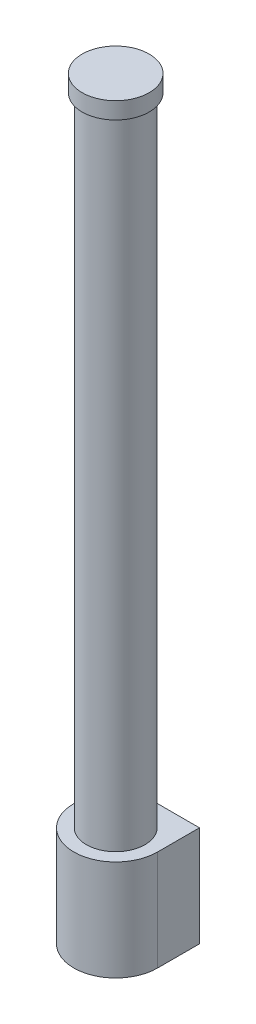
SolidWorks part; units mm, degrees
ref_plane "Front Plane" through (0, 0, 0) normal (0, 0, 1) x (1, 0, 0)
ref_plane "Top Plane" through (0, 0, 0) normal (0, 1, 0) x (1, 0, 0)
ref_plane "Right Plane" through (0, 0, 0) normal (1, 0, 0) x (0, 0, -1)
sketch "Sketch1" plane through (0, 0, 0) normal (0, 1, 0) x (1, 0, 0)
  circle A0 centre (0, 0) radius 22.225
  dimension "D1" = 44.45
extrude "Boss-Extrude1" add sketch "Sketch1" along normal blind 482.6
sketch "Sketch2" plane through (0, 482.6, 0) normal (0, 1, 0) x (1, 0, 0)
  circle A0 centre (0, 0) radius 25.4
  dimension "D1" = 50.8
extrude "Boss-Extrude2" add sketch "Sketch2" along normal blind 12.7
sketch "Sketch3" plane through (0, 0, 0) normal (0, -1, 0) x (1, 0, 0)
  line L0 (-31.75, 0) -> (-31.75, -31.75)
  line L1 (-31.75, -31.75) -> (31.75, -31.75)
  line L2 (31.75, -31.75) -> (31.75, 0)
  arc A0 (-31.75, 0) -> (31.75, 0) centre (0, 0) cw
  point P4 (0, 31.75)
  dimension "D1" = 31.75
  dimension "D2" = 63.5
extrude "Boss-Extrude3" add sketch "Sketch3" along normal blind 76.2
